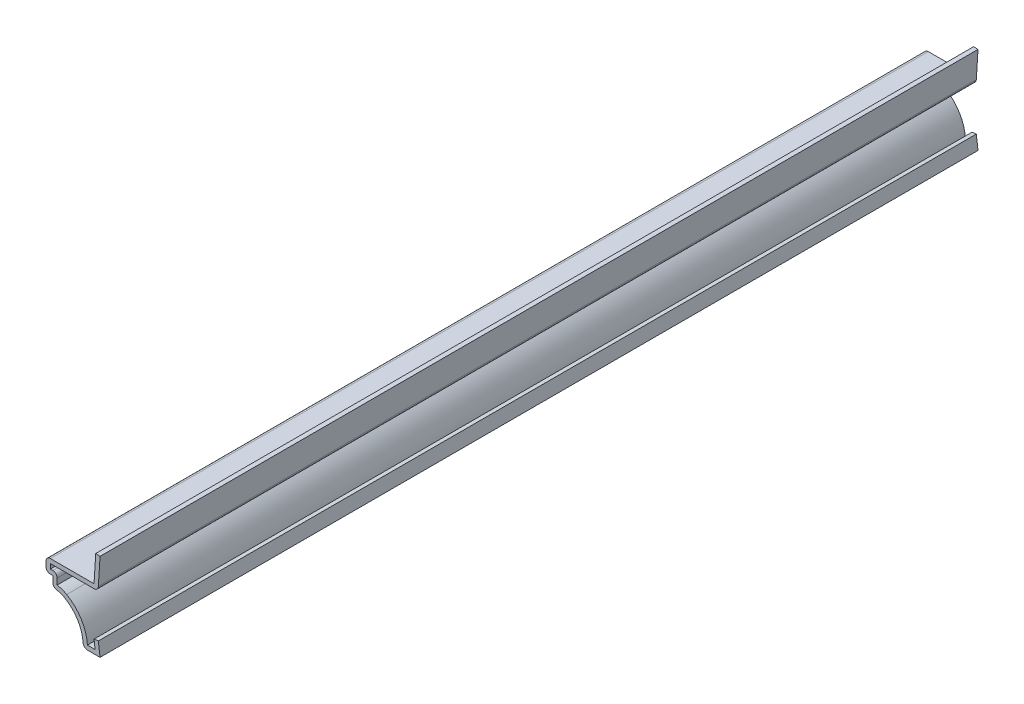
SolidWorks part; units mm, degrees
ref_plane "Front Plane" through (0, 0, 0) normal (0, 0, 1) x (1, 0, 0)
ref_plane "Top Plane" through (0, 0, 0) normal (0, 1, 0) x (1, 0, 0)
ref_plane "Right Plane" through (0, 0, 0) normal (1, 0, 0) x (0, 0, -1)
sketch "Sketch1" plane through (0, 0, 0) normal (0, 0, 1) x (1, 0, 0)
  line L0 (0, 0) -> (0, 20.5741) construction
  line L1 (-1.014, 20.6375) -> (0, 20.5741) construction
  line L2 (-0.3969, 3.1501) -> (0, 0)
  line L3 (0, 0) -> (-3.9688, 0)
  line L4 (-11.1125, 8.7313) -> (-11.1125, 11.1125)
  line L5 (-11.1125, 11.1125) -> (-12.7, 11.1125)
  line L6 (-12.7, 11.1125) -> (-12.7, 14.2875)
  line L7 (-12.7, 14.2875) -> (-1.4109, 14.2875)
  line L8 (-1.4109, 14.2875) -> (-1.014, 20.6375)
  arc A0 (-11.1125, 8.7313) -> (-8.352, 7.997) centre (-11.1125, 3.175) cw
  arc A1 (-8.352, 7.997) -> (-3.9688, 0) centre (-12.6899, 0.4196) cw
  point P8 (0, 0)
  dimension "D8" = 3.9688
  dimension "D12" = 5.5562
  dimension "D13" = 8.7312
  dimension "D1" = 14.2875
  dimension "D2" = 6.35
  dimension "D3" = 0.3969
  dimension "D4" = 1.016
  dimension "D5" = 12.7
  dimension "D6" = 3.175
  dimension "D7" = 2.3813
  dimension "D9" = 3.175
  dimension "D10" = 0.3969
  dimension "D11" = 1.5875
extrude "Extrude-Thin1" add sketch "Sketch1" against normal blind 206.375 thin
fillet "Fillet1" radius 1.016 6 edges at (-3.9688, 0, -103.1875) (-11.1125, 8.7313, -103.1875) (-10.0965, 12.1285, -103.1875) (-12.7, 11.1125, -103.1875) (-12.7, 14.2875, -103.1875) (-0.4564, 13.2715, -103.1875)
